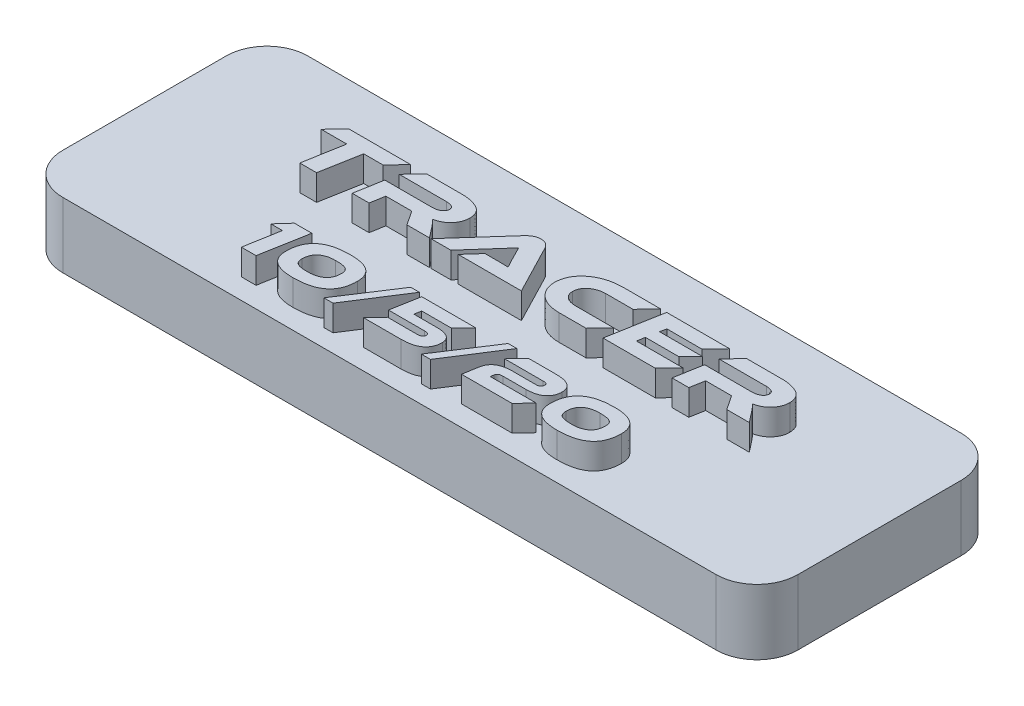
SolidWorks part; units mm, degrees
ref_plane "Front Plane" through (0, 0, 0) normal (0, 0, 1) x (1, 0, 0)
ref_plane "Top Plane" through (0, 0, 0) normal (0, 1, 0) x (1, 0, 0)
ref_plane "Right Plane" through (0, 0, 0) normal (1, 0, 0) x (0, 0, -1)
sketch "Sketch1" plane through (0, 0, 0) normal (0, 1, 0) x (1, 0, 0)
  line L1 (-28.575, 9.525) -> (28.575, 9.525)
  line L2 (-28.575, 9.525) -> (-28.575, -9.525)
  line L3 (-28.575, -9.525) -> (28.575, -9.525)
  line L4 (28.575, 9.525) -> (28.575, -9.525)
  line L5 (-28.575, 9.525) -> (28.575, -9.525) construction
  line L6 (-28.575, -9.525) -> (28.575, 9.525) construction
  point P0 (0, 0)
  dimension "D1" = 57.15
  dimension "D2" = 19.05
extrude "Boss-Extrude1" add sketch "Sketch1" along normal up to surface (5.08 mm away)
fillet "Fillet1" radius 3.175 4 edges at (-28.575, 2.54, 9.525) (-28.575, 2.54, -9.525) (28.575, 2.54, 9.525) (28.575, 2.54, -9.525)
sketch "Sketch3" plane through (0, 5.08, 0) normal (0, 1, 0) x (1, 0, 0)
  line L0 (28.575, -7.9375) -> (-28.575, -7.9375) construction
  line L1 (28.575, -6.35) -> (28.575, 6.35) construction
  line L2 (-28.575, 6.35) -> (-28.575, -6.35) construction
  line L3 (28.575, 0) -> (-28.575, 0) construction
  line L5 (-25.4, -9.525) -> (25.4, -9.525) construction
  line L6 (25.4, 9.525) -> (-25.4, 9.525) construction
  text T0 "TRACER" font "Ethnocentric Rg" height in points 16
  text T1 "10/5/20" font "Ethnocentric Rg" height in points 14
  point P8 (-28.575, 0)
  dimension "D1" = 1.5875
extrude "Boss-Extrude2" add sketch "Sketch3" along normal blind 2
sketch "Sketch4" plane through (0, 0, 0) normal (0, -1, 0) x (1, 0, 0)
  line L0 (25.4, 0) -> (-25.4, 0) construction
  circle A0 centre (-25.4, 0) radius 0.9
  circle A1 centre (25.4, 0) radius 0.9
  point P3 (0, 0)
  dimension "D2" = 1.8
  dimension "D1" = 50.8
extrude "Cut-Extrude1" cut sketch "Sketch4" against normal blind 4
